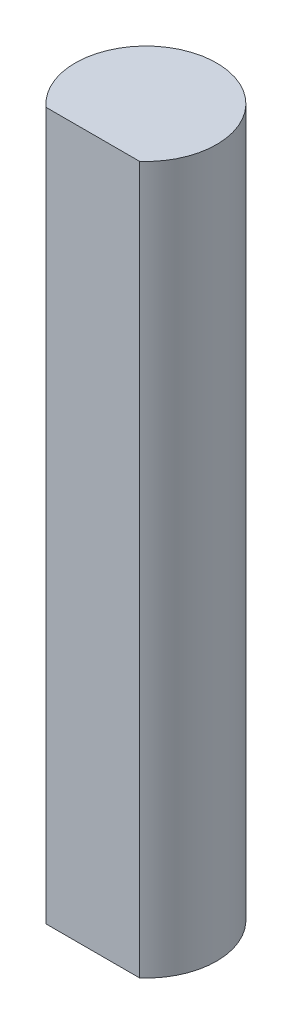
SolidWorks part; units mm, degrees
ref_plane "Front Plane" through (0, 0, 0) normal (0, 0, 1) x (1, 0, 0)
ref_plane "Top Plane" through (0, 0, 0) normal (0, 1, 0) x (1, 0, 0)
ref_plane "Right Plane" through (0, 0, 0) normal (1, 0, 0) x (0, 0, -1)
sketch "Sketch1" plane through (0, 0, 0) normal (0, 1, 0) x (1, 0, 0)
  line L0 (0, 0) -> (0, -4) construction
  line L2 (-4, -3) -> (4, -3)
  line L3 (-4, -3) -> (-4, -4)
  line L4 (-4, -4) -> (4, -4)
  line L5 (4, -3) -> (4, -4)
  line L6 (-4, -3) -> (4, -4) construction
  line L7 (-4, -4) -> (4, -3) construction
  circle A0 centre (0, 0) radius 4
  point P3 (0, -3.5)
  point P9 (0, -4)
  dimension "D1" = 8
  dimension "D2" = 3
  dimension "D3" = 8
extrude "Boss-Extrude1" add sketch "Sketch1" along normal blind 40 contours L2 A0
